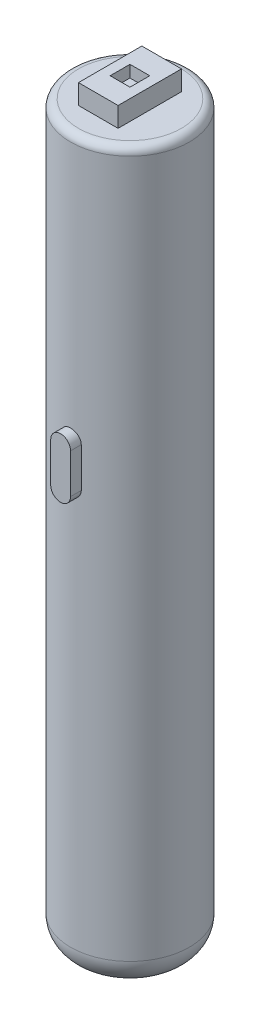
SolidWorks part; units mm, degrees
ref_plane "Front Plane" through (0, 0, 0) normal (0, 0, 1) x (1, 0, 0)
ref_plane "Top Plane" through (0, 0, 0) normal (0, 1, 0) x (1, 0, 0)
ref_plane "Right Plane" through (0, 0, 0) normal (1, 0, 0) x (0, 0, -1)
sketch "Sketch1" plane through (0, 0, 0) normal (0, 1, 0) x (1, 0, 0)
  circle A0 centre (0, 0) radius 15
extrude "Boss-Extrude1" add sketch "Sketch1" along normal blind 185
fillet "Fillet2" radius 7 1 edges at (0, 0, 15)
fillet "Fillet3" radius 2 1 edges at (0, 185, 15)
sketch "Sketch2" plane through (0, 0, 0) normal (0, 1, 0) x (1, 0, 0)
  circle A0 centre (0, 0) radius 6
extrude "Cut-Extrude1" cut sketch "Sketch2" along normal blind 180
ref_plane "Plane1" through (0, 0, 15) normal (0, 0, 1) x (1, 0, 0)
ref_plane "Plane2" through (0, 0, -15) normal (0, 0, 1) x (1, 0, 0)
sketch "Sketch7" plane through (0, 0, 15) normal (0, 0, 1) x (1, 0, 0)
  line L2 (0, 183) -> (0, 7) construction
  line L8 (2.5, 113) -> (2.5, 118)
  line L9 (2.5, 113) -> (2.5, 108)
  line L10 (-2.5, 113) -> (-2.5, 118)
  line L11 (-2.5, 113) -> (-2.5, 108)
  line L13 (2.5, 118) -> (2.5, 108)
  line L14 (-2.5, 118) -> (-2.5, 108.7624)
  arc A0 (2.5, 108) -> (-2.5, 108) centre (0, 108) cw
  arc A1 (2.5, 118) -> (-2.5, 118) centre (0, 118) ccw
extrude "Boss-Extrude3" add sketch "Sketch7" along normal blind 2.5 and the other way blind 32.5 contours L8 A1 L10 L11 A0 L9
sketch "Sketch8" plane through (0, 0, 0) normal (0, 1, 0) x (1, 0, 0)
  line L3 (0, 8) -> (-5, 8)
  line L4 (-5, 0) -> (-5, 8)
  line L7 (0, -8) -> (-5, -8)
  line L8 (-5, 0) -> (-5, -8)
  line L11 (0, -8) -> (5, -8)
  line L12 (5, 0) -> (5, -8)
  line L15 (0, 8) -> (5, 8)
  line L16 (5, 0) -> (5, 8)
extrude "Boss-Extrude4" add sketch "Sketch8" along normal blind 5 from offset 185
ref_plane "Plane3" through (-5, 0, 0) normal (-1, 0, 0) x (0, 0, 1)
sketch "Sketch9" plane through (-5, 0, 0) normal (-1, 0, 0) x (0, 0, 1)
  line L1 (-8, 190) -> (8, 190) construction
  line L2 (0, 192) -> (-0.8141, 192)
  line L3 (0, 192) -> (2.5, 192)
  line L4 (-0.8141, 192) -> (-0.8141, 190)
  line L5 (2.5, 192) -> (2.5, 190)
  line L6 (-0.8141, 190) -> (2.5, 190)
sketch "Sketch10" plane through (0, 190, 0) normal (0, 1, 0) x (1, 0, 0)
  line L1 (-5, 8) -> (-5, -8) construction
  line L4 (-5, 0) -> (-4.7768, 0.0978)
  line L6 (0, 2.6476) -> (0, -5.2953) construction
  line L8 (0, -2.5) -> (2.5, -2.5)
  line L9 (0, 2.5) -> (2.5, 2.5)
  line L10 (0, 2.5) -> (-2.5, 2.5)
  line L11 (0, -2.5) -> (-2.5, -2.5)
  line L12 (-2.5, 2.5) -> (-2.5, -2.5)
  line L13 (2.5, -2.5) -> (2.5, 2.5)
extrude "Cut-Extrude3" cut sketch "Sketch10" against normal blind 3 contours L8 L13 L9 L10 L12 L11
